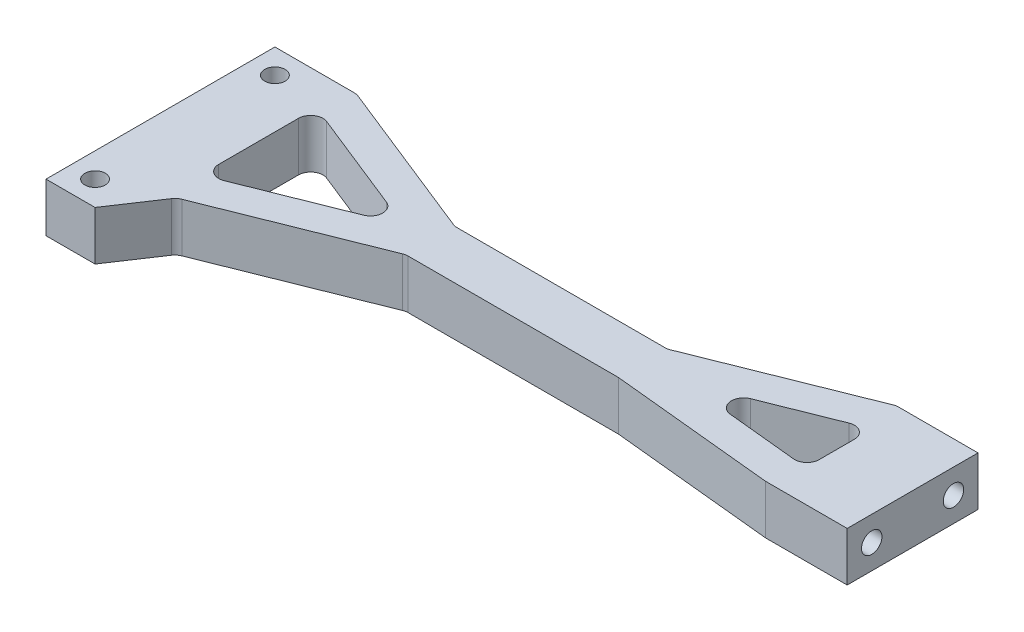
SolidWorks part; units mm, degrees
material "1060 Alloy"
ref_plane "Front Plane" through (0, 0, 0) normal (0, 0, 1) x (1, 0, 0)
ref_plane "Top Plane" through (0, 0, 0) normal (0, 1, 0) x (1, 0, 0)
ref_plane "Right Plane" through (0, 0, 0) normal (1, 0, 0) x (0, 0, -1)
sketch "Sketch2" plane through (0, 0, 0) normal (0, 1, 0) x (1, 0, 0)
  line L0 (56, -8) -> (76, 0)
  line L1 (86, -16) -> (76, -16)
  line L2 (56, -14) -> (30, -14)
  line L3 (10, -22) -> (6, -28)
  line L4 (6, -28) -> (0, -28)
  line L5 (0, -28) -> (0, 0)
  line L6 (86, -16) -> (86, 0)
  line L7 (86, 0) -> (76, 0)
  line L8 (9, -3.9081) -> (26.7297, -11)
  line L9 (56, -8) -> (30, -8)
  line L10 (76, -16) -> (56, -14)
  line L11 (10, 0) -> (0, 0)
  line L12 (30, -14) -> (10, -22)
  line L13 (30, -8) -> (10, 0)
  line L14 (26.7297, -11) -> (9, -18.0919)
  line L15 (9, -18.0919) -> (9, -3.9081)
  line L17 (60.6562, -10.4457) -> (77, -12.08)
  line L18 (77, -12.08) -> (77, -3.9081)
  line L19 (77, -3.9081) -> (60.6562, -10.4457)
  dimension "D1" = 6
  dimension "D2" = 86
  dimension "D3" = 6
  dimension "D4" = 10
  dimension "D5" = 28
  dimension "D6" = 10
  dimension "D7" = 20
  dimension "D8" = 20
  dimension "D9" = 16
  dimension "D10" = 4
  dimension "D11" = 4
  dimension "D12" = 4
  dimension "D13" = 4
  dimension "D14" = 8
  dimension "D15" = 9
  dimension "D16" = 9
  dimension "D17" = 8
extrude "Boss-Extrude1" add sketch "Sketch2" along normal blind 6
hole_wizard "Tap Drill for M3 Tap3" positions "Sketch8" profile "Sketch7" hole size "M3" standard "ISO"
sketch "Sketch8" plane through (0, 6, 0) normal (0, 1, 0) x (1, 0, 0)
  line L2 (0, -28) -> (6, -28) construction
  line L4 (0, 0) -> (0, -28) construction
  line L6 (10, 0) -> (0, 0) construction
  point P0 (3, -3)
  point P2 (3, -25)
  dimension "D1" = 3
  dimension "D2" = 3
  dimension "D3" = 3
  dimension "D4" = 3
sketch "Sketch7" plane through (3, 6, 3) normal (1, 0, 0) x (0, 0, 1)
  line L0 (0, 0) -> (0, 10.7511)
  line L1 (0, 10.7511) -> (1.25, 10)
  line L2 (1.25, 10) -> (1.25, 0)
  line L5 (1.25, 0) -> (0, 0)
  line L10 (0, 10.7511) -> (-1.25, 10) construction
  line L11 (0, -6.35) -> (0, 107.95) construction
  dimension "Hole Dia." = 2.5
  dimension "Hole Depth" = 10
  dimension "Drill Angle" = 118
hole_wizard "Tap Drill for M3 Tap2" positions "Sketch6" profile "Sketch5" hole size "M3" standard "ISO"
sketch "Sketch6" plane through (86, 0.7792, 7.6405) normal (1, 0, 0) x (0, 0, -1)
  line L4 (-8.3595, -0.7792) -> (7.6405, -0.7792) construction
  line L5 (7.6405, 5.2208) -> (7.6405, -0.7792) construction
  point P0 (-5.3595, 2.2208)
  point P2 (4.6405, 2.2208)
  dimension "D1" = 3
  dimension "D2" = 3
  dimension "D3" = 10
sketch "Sketch5" plane through (86, 3, 13) normal (0, 1, 0) x (0, 0, -1)
  line L0 (0, 0) -> (0, 8.7511)
  line L1 (0, 8.7511) -> (1.25, 8)
  line L2 (1.25, 8) -> (1.25, 0)
  line L5 (1.25, 0) -> (0, 0)
  line L10 (0, 8.7511) -> (-1.25, 8) construction
  line L11 (0, -6.35) -> (0, 107.95) construction
  dimension "Hole Dia." = 2.5
  dimension "Hole Depth" = 8
  dimension "Drill Angle" = 118
hole_wizard "Tap Drill for M3 Tap1" positions "Sketch4" profile "Sketch3" hole size "M3" standard "ISO"
sketch "Sketch4" plane through (0, 0, 0) normal (-1, 0, 0) x (0, 0, 1)
  line L0 (0, 0) -> (28, 0) construction
  line L2 (0, 6) -> (0, 0) construction
  point P0 (8, 3)
  point P2 (18, 3)
  dimension "D1" = 3
  dimension "D2" = 8
  dimension "D3" = 10
sketch "Sketch3" plane through (0, 3, 8) normal (0, 1, 0) x (0, 0, 1)
  line L0 (0, 0) -> (0, 8.7511)
  line L1 (0, 8.7511) -> (1.25, 8)
  line L2 (1.25, 8) -> (1.25, 0)
  line L5 (1.25, 0) -> (0, 0)
  line L10 (0, 8.7511) -> (-1.25, 8) construction
  line L11 (0, -6.35) -> (0, 107.95) construction
  dimension "Hole Dia." = 2.5
  dimension "Hole Depth" = 8
  dimension "Drill Angle" = 118
fillet "Fillet1" radius 1.5 12 edges at (76, 3, 0) (56, 3, 8) (60.6562, 3, 10.4457) (77, 3, 12.08) (77, 3, 3.9081) (30, 3, 14) (10, 3, 22) (30, 3, 8) (10, 3, 0) (9, 3, 18.0919) (26.7297, 3, 11) (9, 3, 3.9081)
